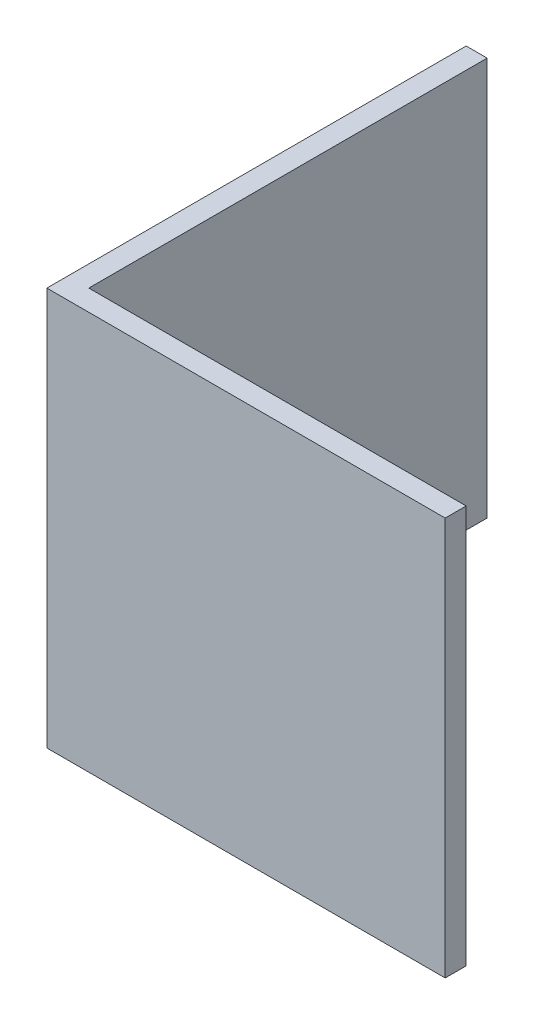
SolidWorks part; units mm, degrees
material "1060 Сплав"
ref_plane "Спереди" through (0, 0, 0) normal (0, 0, 1) x (1, 0, 0)
ref_plane "Сверху" through (0, 0, 0) normal (0, 1, 0) x (1, 0, 0)
ref_plane "Справа" through (0, 0, 0) normal (1, 0, 0) x (0, 0, -1)
sketch "Эскиз1" plane through (0, 0, 0) normal (0, 1, 0) x (1, 0, 0)
  line L0 (0, 0) -> (0, 20)
  line L1 (0, 20) -> (1, 20)
  line L2 (1, 20) -> (1, 1)
  line L3 (1, 1) -> (20, 1)
  line L4 (20, 1) -> (20, 0)
  line L5 (20, 0) -> (0, 0)
  dimension "D1" = 1
  dimension "D2" = 20
extrude "Бобышка-Вытянуть1" add sketch "Эскиз1" along normal blind 19
sketch "Эскиз2" plane through (20, 0, 0) normal (1, 0, 0) x (0, 0, -1)
  line L4 (0, 0) -> (1, 0)
  line L5 (1, 0) -> (1, 19)
  line L6 (1, 19) -> (0, 19)
  line L7 (0, 19) -> (0, 0)
  line L8 (0, 0) -> (1, 0)
  line L9 (1, 0) -> (1, 19)
  line L10 (1, 19) -> (0, 19)
  line L11 (0, 19) -> (0, 0)
  dimension "D1" = 0
extrude "Вырез-Вытянуть1" cut sketch "Эскиз2" against normal blind 1
